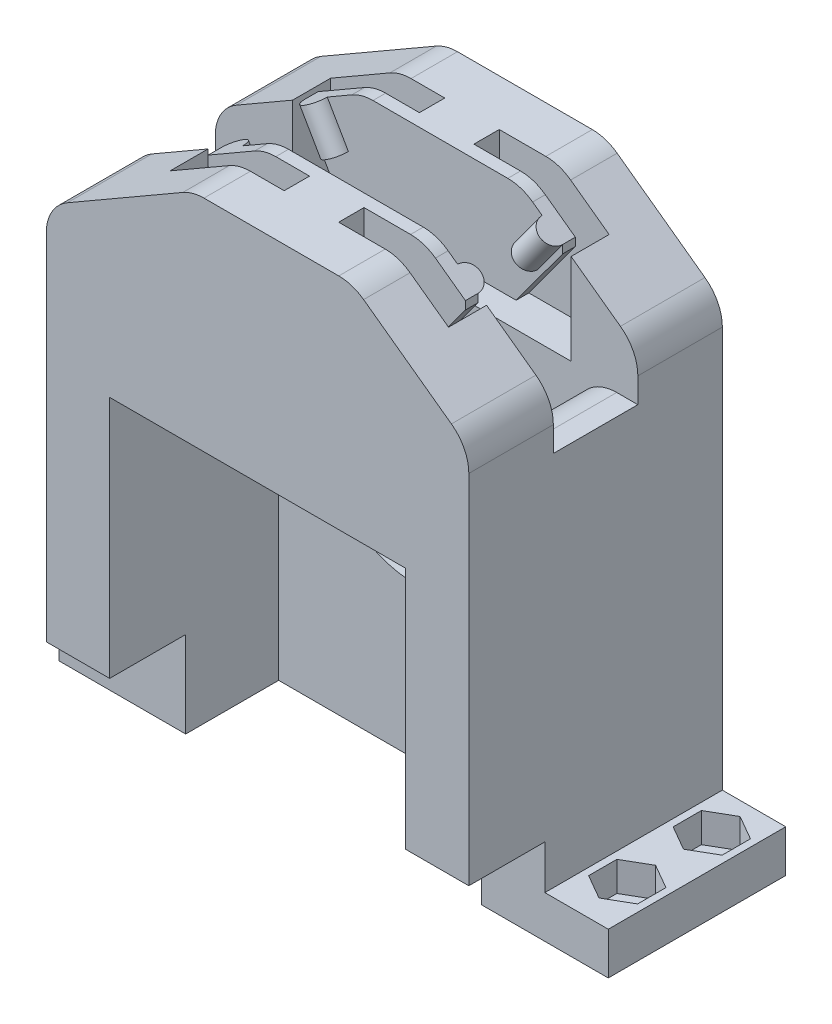
SolidWorks part; units mm, degrees
ref_plane "Front Plane" through (0, 0, 0) normal (0, 0, 1) x (1, 0, 0)
ref_plane "Top Plane" through (0, 0, 0) normal (0, 1, 0) x (1, 0, 0)
ref_plane "Right Plane" through (0, 0, 0) normal (1, 0, 0) x (0, 0, -1)
sketch "Sketch1" plane through (0, 0, 0) normal (0, 0, 1) x (1, 0, 0)
  line L0 (0.5834, 17.8723) -> (-16.7371, 7.8723)
  line L1 (-16.7371, 17.8723) -> (33.2629, 17.8723)
  line L2 (-16.7371, 17.8723) -> (-16.7371, -47.1277)
  line L3 (-16.7371, -47.1277) -> (33.2629, -47.1277)
  line L4 (33.2629, 17.8723) -> (33.2629, -47.1277)
  line L5 (19.4991, 17.8723) -> (33.2629, 7.8723)
  dimension "D1" = 50
  dimension "D2" = 65
  dimension "D3" = 0
  dimension "D4" = 0
  dimension "D5" = 60
  dimension "D6" = 0
  dimension "D7" = 0
  dimension "D8" = 54
  dimension "D9" = 10
  dimension "D10" = 10
extrude "Boss-Extrude1" add sketch "Sketch1" along normal blind 30 contours L5 L1 L0 L2 L3 L4
sketch "Sketch2" plane through (0, 17.8723, 0) normal (0, 1, 0) x (1, 0, 0)
  line L0 (0.5834, 0) -> (19.4991, 0) construction
  line L1 (-16.7371, -10) -> (33.2629, -10)
  line L2 (-16.7371, -10) -> (-16.7371, -20)
  line L3 (-16.7371, -20) -> (33.2629, -20)
  line L4 (33.2629, -10) -> (33.2629, -20)
  line L5 (0.5834, -30) -> (19.4991, -30) construction
  line L6 (33.2629, -30) -> (33.2629, 0) construction
  line L7 (-16.7371, -30) -> (-16.7371, 0) construction
  dimension "D1" = 10
  dimension "D2" = 10
  dimension "D3" = 0
  dimension "D4" = 0
extrude "Cut-Extrude1" cut sketch "Sketch2" against normal blind 25
sketch "Sketch3" plane through (0, -47.1277, 0) normal (0, -1, 0) x (1, 0, 0)
  line L0 (-16.7371, 30) -> (33.2629, 30) construction
  line L1 (-9.2371, 20) -> (25.7629, 20)
  line L2 (-9.2371, 20) -> (-9.2371, 10)
  line L3 (-9.2371, 10) -> (25.7629, 10)
  line L4 (25.7629, 20) -> (25.7629, 10)
  line L5 (-16.7371, 0) -> (33.2629, 0) construction
  line L6 (33.2629, 30) -> (33.2629, 0) construction
  line L7 (-16.7371, 30) -> (-16.7371, 0) construction
  dimension "D1" = 10
  dimension "D2" = 10
  dimension "D3" = 7.5
  dimension "D4" = 7.5
sketch "Sketch4" plane through (-7.5931, 13.1516, 0) normal (-0.5, 0.866, 0) x (0, 0, 1)
  line L0 (10, -10.5586) -> (10, 9.4414) construction
  line L1 (10, -10.5586) -> (0, -10.5586) construction
  line L2 (20, 9.4414) -> (20, -10.5586) construction
  line L3 (30, -10.5586) -> (20, -10.5586) construction
  circle A0 centre (10, 3.2414) radius 1.5
  circle A1 centre (20, 3.2414) radius 1.5
  dimension "D2" = 13.8
  dimension "D5" = 3
  dimension "D6" = 13.8
  dimension "D1" = 0
  dimension "D3" = 0
extrude "Boss-Extrude2" add sketch "Sketch4" against normal blind 5
sketch "Sketch6" plane through (0, 17.8723, 0) normal (0, 1, 0) x (1, 0, 0)
  line L0 (19.4991, -10) -> (0.5834, -10) construction
  line L1 (-6.085, -5.5) -> (5.915, -5.5)
  line L2 (-6.085, -5.5) -> (-6.085, -8.5)
  line L3 (-6.085, -8.5) -> (5.915, -8.5)
  line L4 (5.915, -5.5) -> (5.915, -8.5)
  line L5 (-16.7371, -10) -> (-6.085, -10) construction
  line L6 (-6.085, -5.5) -> (-7.585, -5.5)
  line L7 (-6.085, -5.5) -> (-6.085, -10)
  line L8 (-6.085, -10) -> (-7.585, -10)
  line L9 (-7.585, -5.5) -> (-7.585, -10)
  line L10 (-6.085, -20) -> (-16.7371, -20) construction
  line L11 (-6.085, -21.5) -> (5.915, -21.5)
  line L12 (-6.085, -21.5) -> (-6.085, -24.5)
  line L13 (-6.085, -24.5) -> (5.915, -24.5)
  line L14 (5.915, -21.5) -> (5.915, -24.5)
  line L15 (-7.585, -20) -> (-6.085, -20)
  line L16 (-7.585, -20) -> (-7.585, -24.5)
  line L17 (-7.585, -24.5) -> (-6.085, -24.5)
  line L18 (-6.085, -20) -> (-6.085, -24.5)
  line L19 (0.5834, -20) -> (19.4991, -20) construction
  line M8 (0.5834, 0) -> (0.5834, -10)
  dimension "D1" = 0
  dimension "D2" = 3
  dimension "D3" = 12
  dimension "D4" = 1.5
  dimension "D5" = 0
  dimension "D6" = 0
  dimension "D7" = 1.5
  dimension "D8" = 0
  dimension "D9" = 0
  dimension "D10" = 0
  dimension "D11" = 1.5
  dimension "D12" = 0
  dimension "D13" = 0
  dimension "D14" = 1.5
  dimension "D15" = 3
  dimension "D16" = 12
extrude "Cut-Extrude15" cut sketch "Sketch6" against normal blind 15 contours L4 L1 L3 M8 | L2 L3 L1 M8 | L14 L11 L12 L13 | L18 L15 L16 L17 L12 | L9 L8 L7 L6
sketch "Sketch7" plane through (0, 0, 10) normal (0, 0, 1) x (1, 0, 0)
  line L0 (-6.085, 2.8723) -> (-7.585, 2.8723) construction
  line L1 (-6.085, 5.8723) -> (24.415, 5.8723)
  line L2 (-6.085, 5.8723) -> (-6.085, 2.8723)
  line L3 (-6.085, 2.8723) -> (24.415, 2.8723)
  line L4 (24.415, 5.8723) -> (24.415, 2.8723)
  line L6 (-6.085, 2.8723) -> (-6.085, 14.0223) construction
  dimension "D1" = 0
  dimension "D2" = 0
  dimension "D3" = 3
  dimension "D4" = 30.5
extrude "Cut-Extrude16" cut sketch "Sketch7" against normal blind 3 and the other way blind 13
sketch "Sketch8" plane through (0, 0, 30) normal (0, 0, 1) x (1, 0, 0)
  line L0 (-16.7371, -47.1277) -> (33.2629, -47.1277) construction
  line L1 (-9.2371, -8.1277) -> (25.7629, -8.1277)
  line L2 (-9.2371, -8.1277) -> (-9.2371, -47.1277)
  line L3 (-9.2371, -47.1277) -> (25.7629, -47.1277)
  line L4 (25.7629, -8.1277) -> (25.7629, -47.1277)
  line L5 (33.2629, 7.8723) -> (33.2629, -47.1277) construction
  line L6 (-16.7371, 7.8723) -> (-16.7371, -47.1277) construction
  point P6 (33.2629, -19.6277)
  dimension "D1" = 0
  dimension "D2" = 39
  dimension "D3" = 7.5
  dimension "D4" = 7.5
extrude "Cut-Extrude17" cut sketch "Sketch8" against normal up to surface (10 mm away) up to face at (4.4377, 7.8872, 20)
sketch "Sketch9" plane through (0, 0, 10) normal (0, 0, 1) x (1, 0, 0)
  line L1 (25.7629, -47.1277) -> (-9.2371, -47.1277) construction
  circle A0 centre (6.8891, -18.1277) radius 11.05
  dimension "D1" = 22.1
  dimension "D2" = 29
extrude "Cut-Extrude18" cut sketch "Sketch3" against normal up to surface (40 mm away) up to face at (8.2629, -7.1277, 15)
extrude "Cut-Extrude19" cut sketch "Sketch9" against normal blind 8
fillet "Fillet5" radius 5 1 edges at (-16.7371, 7.8723, 5)
fillet "Fillet6" radius 5 1 edges at (-16.7371, 7.8723, 25)
fillet "Fillet7" radius 5 1 edges at (0.5834, 17.8723, 2.75)
fillet "Fillet8" radius 5 2 edges at (0.5834, 17.8723, 9.25)
fillet "Fillet9" radius 5 1 edges at (0.5834, 17.8723, 20.75)
fillet "Fillet10" radius 5 1 edges at (0.5834, 17.8723, 27.25)
sketch "Sketch10" plane through (33.2629, 0, 0) normal (1, 0, 0) x (0, 0, -1)
  line L0 (-30, -47.1277) -> (0, -47.1277) construction
  line L1 (-30, -36.9277) -> (-21, -36.9277)
  line L2 (-30, -36.9277) -> (-30, -47.1277)
  line L3 (-30, -47.1277) -> (-21, -47.1277)
  line L4 (-21, -36.9277) -> (-21, -47.1277)
  line L5 (-30, 7.8723) -> (-30, -47.1277) construction
  dimension "D1" = 0
  dimension "D2" = 0
  dimension "D3" = 9
  dimension "D4" = 10.2
extrude "Cut-Extrude20" cut sketch "Sketch10" against normal through all
sketch "Sketch11" plane through (15.2355, 20.9699, 0) normal (0.5878, 0.809, 0) x (0, 0, -1)
  line L0 (-20, -5.27) -> (-20, -22.2831) construction
  line L1 (-10, -22.2831) -> (-10, -5.27) construction
  line L2 (-10, -22.2831) -> (0, -22.2831) construction
  line L3 (-30, -22.2831) -> (-20, -22.2831) construction
  circle A0 centre (-20, -9.7831) radius 1.5
  circle A1 centre (-10, -9.7831) radius 1.5
  dimension "D2" = 3
  dimension "D4" = 3
  dimension "D6" = 12.5
  dimension "D1" = 0
  dimension "D3" = 0
  dimension "D5" = 12.5
extrude "Boss-Extrude3" add sketch "Sketch11" against normal blind 5
sketch "Sketch13" plane through (0, 17.8723, 0) normal (0, 1, 0) x (1, 0, 0)
  line L1 (12.3637, -24.5) -> (24.3637, -24.5)
  line L2 (12.3637, -24.5) -> (12.3637, -21.5)
  line L3 (12.3637, -21.5) -> (24.3637, -21.5)
  line L4 (24.3637, -24.5) -> (24.3637, -21.5)
  line L5 (24.3637, -24.5) -> (25.3637, -24.5)
  line L6 (24.3637, -24.5) -> (24.3637, -14.9293)
  line L7 (24.3637, -14.9293) -> (25.3637, -14.9293)
  line L8 (25.3637, -24.5) -> (25.3637, -14.9293)
  line L9 (12.3637, -8.5) -> (24.3637, -8.5)
  line L10 (12.3637, -8.5) -> (12.3637, -5.5)
  line L11 (12.3637, -5.5) -> (24.3637, -5.5)
  line L12 (24.3637, -8.5) -> (24.3637, -5.5)
  line L13 (24.3637, -11.2788) -> (25.3637, -11.2788)
  line L14 (24.3637, -11.2788) -> (24.3637, -5.5)
  line L15 (24.3637, -5.5) -> (25.3637, -5.5)
  line L16 (25.3637, -11.2788) -> (25.3637, -5.5)
  line L17 (1.9232, -20) -> (19.4991, -20) construction
  line L18 (19.4991, -10) -> (1.9232, -10) construction
  line M4 (19.4991, -30) -> (19.4991, -20)
  dimension "D1" = 3
  dimension "D2" = 1.5
  dimension "D3" = 0
  dimension "D4" = 0
  dimension "D5" = 0
  dimension "D6" = 1
  dimension "D7" = 1
  dimension "D8" = 0
  dimension "D9" = 3
  dimension "D10" = 1.5
  dimension "D11" = 0
  dimension "D12" = 0
  dimension "D13" = 12
  dimension "D14" = 12
extrude "Cut-Extrude22" cut sketch "Sketch13" against normal blind 15 contours L3 L2 L1 M4 | L1 L4 L3 M4 | L5 L8 L7 L6 L4 | L13 L16 L15 L12 L14 | L9 L12 L11 L10
sketch "Sketch14" plane through (-16.7371, 0, 0) normal (-1, 0, 0) x (0, 0, 1)
  line L0 (21, -47.1277) -> (21, -36.9277) construction
  line L1 (0, -42.1277) -> (21, -42.1277)
  line L2 (0, -42.1277) -> (0, -47.1277)
  line L3 (0, -47.1277) -> (21, -47.1277)
  line L4 (21, -42.1277) -> (21, -47.1277)
  line L5 (21, -47.1277) -> (0, -47.1277) construction
  line L6 (0, 4.9855) -> (0, -47.1277) construction
  dimension "D1" = 5
  dimension "D2" = 0
  dimension "D3" = 0
  dimension "D4" = 0
extrude "Boss-Extrude4" add sketch "Sketch14" along normal blind 7.5
sketch "Sketch15" plane through (33.2629, 0, 0) normal (1, 0, 0) x (0, 0, -1)
  line L0 (-21, -47.1277) -> (-21, -36.9277) construction
  line L1 (-21, -42.1277) -> (0, -42.1277)
  line L2 (-21, -42.1277) -> (-21, -47.1277)
  line L3 (-21, -47.1277) -> (0, -47.1277)
  line L4 (0, -42.1277) -> (0, -47.1277)
  line L5 (-21, -47.1277) -> (0, -47.1277) construction
  line L6 (0, 7.8723) -> (0, -47.1277) construction
  dimension "D1" = 0
  dimension "D2" = 0
  dimension "D3" = 0
  dimension "D4" = 5
extrude "Boss-Extrude5" add sketch "Sketch15" along normal blind 7.5
sketch "Sketch16" plane through (0, -42.1277, 0) normal (0, 1, 0) x (1, 0, 0)
  line L0 (40.7629, 0) -> (40.7629, -21) construction
  line L1 (37.0129, -11.6514) -> (34.1129, -13.3257)
  line L2 (34.1129, -13.3257) -> (34.1129, -16.6743)
  line L3 (34.1129, -16.6743) -> (37.0129, -18.3486)
  line L4 (37.0129, -18.3486) -> (39.9129, -16.6743)
  line L5 (39.9129, -16.6743) -> (39.9129, -13.3257)
  line L6 (39.9129, -13.3257) -> (37.0129, -11.6514)
  line L7 (37.0129, -1.6514) -> (34.1129, -3.3257)
  line L8 (34.1129, -3.3257) -> (34.1129, -6.6743)
  line L9 (34.1129, -6.6743) -> (37.0129, -8.3486)
  line L10 (37.0129, -8.3486) -> (39.9129, -6.6743)
  line L11 (39.9129, -6.6743) -> (39.9129, -3.3257)
  line L12 (39.9129, -3.3257) -> (37.0129, -1.6514)
  line L13 (40.7629, 0) -> (33.2629, 0) construction
  circle A0 centre (37.0129, -15) radius 2.9 construction
  circle A1 centre (37.0129, -5) radius 2.9 construction
  dimension "D3" = 5.8
  dimension "D4" = 5.8
  dimension "D7" = 5
  dimension "D8" = 10
  dimension "D1" = 0
  dimension "D2" = 0
  dimension "D5" = 3.75
  dimension "D6" = 3.75
extrude "Cut-Extrude23" cut sketch "Sketch16" against normal blind 3.5
sketch "Sketch17" plane through (0, -45.6277, 0) normal (0, 1, 0) x (1, 0, 0)
  line L1 (40.7629, 0) -> (40.7629, -21) construction
  line L2 (40.7629, 0) -> (33.2629, 0) construction
  circle A0 centre (37.0129, -15) radius 1.425
  circle A1 centre (37.0129, -5) radius 1.425
  dimension "D1" = 2.85
  dimension "D2" = 2.85
  dimension "D3" = 3.75
  dimension "D4" = 3.75
  dimension "D5" = 5
  dimension "D6" = 10
extrude "Cut-Extrude24" cut sketch "Sketch17" against normal through all
sketch "Sketch19" plane through (0, -7.1277, 0) normal (0, 1, 0) x (1, 0, 0)
  line L0 (-9.2371, -20) -> (-9.2371, -10) construction
  line L1 (-9.2371, -10) -> (-16.7371, -10)
  line L2 (-9.2371, -10) -> (-9.2371, -20)
  line L3 (-9.2371, -20) -> (-16.7371, -20)
  line L4 (-16.7371, -10) -> (-16.7371, -20)
  line L5 (33.2629, -10) -> (25.7629, -10)
  line L6 (33.2629, -10) -> (33.2629, -20)
  line L7 (33.2629, -20) -> (25.7629, -20)
  line L8 (25.7629, -10) -> (25.7629, -20)
  line L9 (-9.2371, -10) -> (-16.7371, -10) construction
  line L10 (-16.7371, -10) -> (-16.7371, -20) construction
  line L11 (-16.7371, -20) -> (-9.2371, -20) construction
  line L12 (33.2629, -10) -> (25.7629, -10) construction
  line L13 (33.2629, -20) -> (33.2629, -10) construction
  line L14 (25.7629, -10) -> (25.7629, -20) construction
  line L15 (25.7629, -20) -> (33.2629, -20) construction
  dimension "D1" = 0
  dimension "D2" = 0
  dimension "D3" = 0
  dimension "D4" = 0
  dimension "D5" = 0
  dimension "D6" = 0
  dimension "D7" = 0
  dimension "D8" = 0
extrude "Boss-Extrude7" add sketch "Sketch19" along normal blind 9.5
fillet "Fillet14" radius 5 1 edges at (-9.2371, 2.3723, 15)
fillet "Fillet18" radius 5 1 edges at (25.7629, 2.3723, 15)
fillet "Fillet19" radius 5 2 edges at (33.2629, 7.8723, 5)
fillet "Fillet20" radius 5 1 edges at (33.2629, 7.8723, 25)
fillet "Fillet21" radius 5 1 edges at (19.4991, 17.8723, 2.75)
fillet "Fillet22" radius 5 1 edges at (19.4991, 17.8723, 9.25)
fillet "Fillet23" radius 5 1 edges at (19.4991, 17.8723, 27.25)
fillet "Fillet24" radius 5 1 edges at (19.4991, 17.8723, 20.75)
sketch "Sketch20" plane through (0, -42.1277, 0) normal (0, 1, 0) x (1, 0, 0)
  line L0 (-24.2371, -21) -> (-16.7371, -21) construction
  line L1 (-24.2371, -21) -> (-24.2371, 0) construction
  circle A0 centre (-20.5371, -11) radius 1.375
  dimension "D1" = 2.75
  dimension "D2" = 10
  dimension "D3" = 3.7
extrude "Cut-Extrude25" cut sketch "Sketch20" against normal blind 10
sketch "Sketch21" plane through (0, 0, 2) normal (0, 0, 1) x (1, 0, 0)
  circle A0 centre (6.8891, -18.1277) radius 5.5
  circle A1 centre (6.8891, -18.1277) radius 11.05 construction
  dimension "D1" = 0
  dimension "D2" = 11
extrude "Cut-Extrude26" cut sketch "Sketch21" against normal blind 10
sketch "Sketch22" plane through (0, 0, 10) normal (0, 0, 1) x (1, 0, 0)
  line L0 (-6.085, 12.8723) -> (-6.085, 5.8723)
  line L1 (-6.085, 5.8723) -> (-2.085, 5.8723)
  line L2 (-2.085, 5.8723) -> (-6.085, 12.8723)
  line L3 (24.3637, 13.3723) -> (18.8637, 5.8723)
  line L4 (18.8637, 5.8723) -> (24.3637, 5.8723)
  line L5 (24.3637, 5.8723) -> (24.3637, 13.3723)
  line L8 (-6.085, 5.8723) -> (-6.085, 14.0223) construction
  line L11 (24.3637, 14.3379) -> (24.3637, 5.8723) construction
  line L12 (24.3637, 5.8723) -> (-6.085, 5.8723) construction
  line M9 (-6.085, 14.0223) -> (-6.085, 5.8723)
  line M10 (-6.085, 5.8723) -> (24.3637, 5.8723)
  line M11 (24.3637, 5.8723) -> (24.3637, 14.3379)
  dimension "D1" = 0
  dimension "D2" = 7
  dimension "D3" = 0
  dimension "D4" = 4
  dimension "D5" = 0
  dimension "D6" = 0
  dimension "D7" = 7.5
  dimension "D8" = 5.5
extrude "Cut-Extrude27" cut sketch "Sketch22" against normal blind 3 and the other way blind 14 contours L2 M10 M9 | L3 M11 M10
